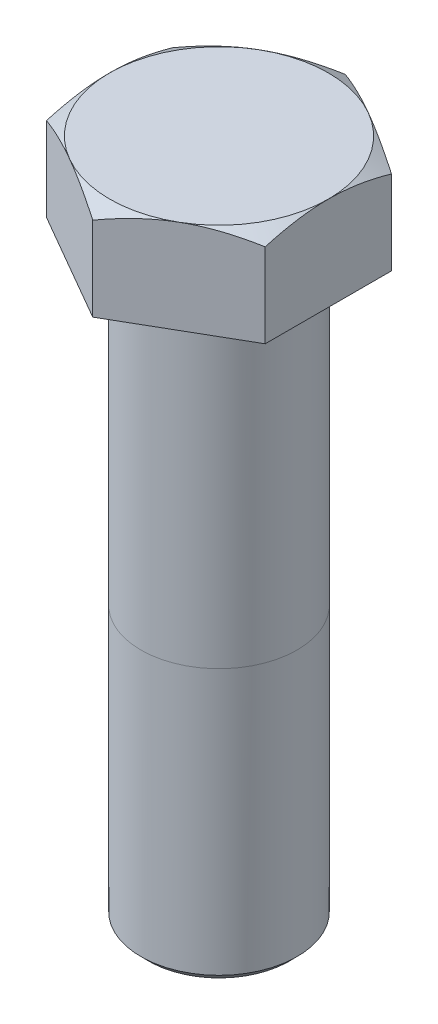
SolidWorks part; units mm, degrees
ref_plane "Front Plane" through (0, 0, 0) normal (0, 0, 1) x (1, 0, 0)
ref_plane "Top Plane" through (0, 0, 0) normal (0, 1, 0) x (1, 0, 0)
ref_plane "Right Plane" through (0, 0, 0) normal (1, 0, 0) x (0, 0, -1)
sketch "Sketch1" plane through (0, 0, 0) normal (0, 1, 0) x (1, 0, 0)
  line L1 (0, 16.1658) -> (-14, 8.0829)
  line L2 (-14, 8.0829) -> (-14, -8.0829)
  line L3 (-14, -8.0829) -> (0, -16.1658)
  line L4 (0, -16.1658) -> (14, -8.0829)
  line L5 (14, -8.0829) -> (14, 8.0829)
  line L6 (14, 8.0829) -> (0, 16.1658)
  circle A0 centre (0, 0) radius 14 construction
  dimension "D1" = 28
extrude "Boss-Extrude1" add sketch "Sketch1" along normal blind 12
sketch "Sketch2" plane through (0, 12, 0) normal (0, 1, 0) x (1, 0, 0)
  line L0 (14, 8.0829) -> (0, 16.1658) construction
  circle A0 centre (0, 0) radius 14
extrude "Cut-Extrude1" cut sketch "Sketch2" against normal blind 12 draft 60 flip side to cut
sketch "Sketch3" plane through (0, 0, 0) normal (0, -1, 0) x (1, 0, 0)
  circle A0 centre (0, 0) radius 10
  dimension "D1" = 20
extrude "Boss-Extrude2" add sketch "Sketch3" along normal blind 75
chamfer "Chamfer1" distance 1 angle 45 1 edges at (0, -75, -10)
sketch "Sketch4" plane through (0, 0, 0) normal (0, 0, 1) x (1, 0, 0)
  line L0 (-10, -40) -> (10, -40)
  line L1 (-10, 0) -> (-10, -74) construction
  line L2 (10, -74) -> (10, 0) construction
  line L3 (-10, 0) -> (10, 0) construction
  dimension "D1" = 40
split line "Split Line1"
